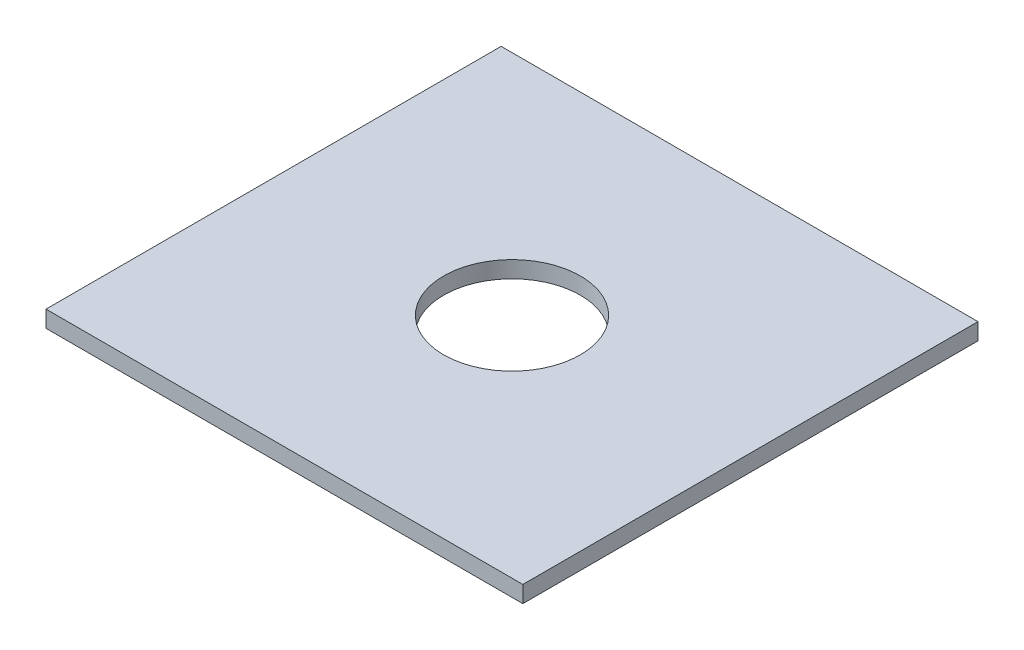
SolidWorks part; units mm, degrees
ref_plane "Alzado" through (0, 0, 0) normal (0, 0, 1) x (1, 0, 0)
ref_plane "Planta" through (0, 0, 0) normal (0, 1, 0) x (1, 0, 0)
ref_plane "Vista lateral" through (0, 0, 0) normal (1, 0, 0) x (0, 0, -1)
sketch "Croquis1" plane through (0, 0, 0) normal (0, 1, 0) x (1, 0, 0)
  line L1 (143, -136.5) -> (-143, -136.5)
  line L2 (143, -136.5) -> (143, 136.5)
  line L3 (143, 136.5) -> (-143, 136.5)
  line L4 (-143, -136.5) -> (-143, 136.5)
  line L5 (143, -136.5) -> (-143, 136.5) construction
  line L6 (143, 136.5) -> (-143, -136.5) construction
  circle A0 centre (0, 0) radius 41
  point P0 (0, 0)
  dimension "D1" = 273
  dimension "D2" = 286
extrude "Saliente-Extruir1" add sketch "Croquis1" along normal blind 10
sketch "Croquis2" plane through (0, 10, 0) normal (0, 1, 0) x (1, 0, 0)
  line L0 (143, 136.5) -> (-143, 136.5) construction
  line L1 (-143, 136.5) -> (-143, -136.5) construction
  circle A0 centre (-93, 86.5) radius 50 construction
  dimension "D1" = 100
